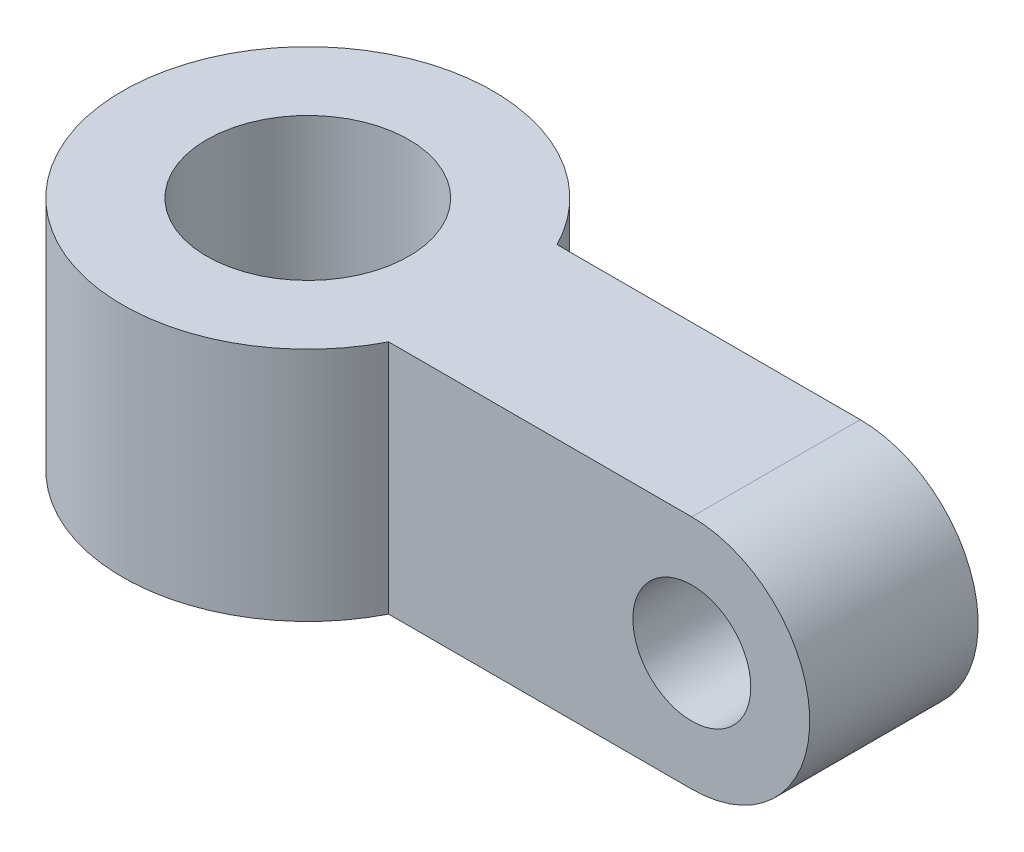
SolidWorks part; units mm, degrees
ref_plane "Plano frontal" through (0, 0, 0) normal (0, 0, 1) x (1, 0, 0)
ref_plane "Plano superior" through (0, 0, 0) normal (0, 1, 0) x (1, 0, 0)
ref_plane "Plano direito" through (0, 0, 0) normal (1, 0, 0) x (0, 0, -1)
sketch "Esboço1" plane through (0, 0, 0) normal (0, 0, 1) x (1, 0, 0)
  line L0 (-1.75, 0) -> (-6, 0) construction
  line L1 (0, 3.5) -> (-6, 3.5)
  line L2 (0, -3.5) -> (-6, -3.5)
  line L3 (-1.75, 3.5) -> (-6, 3.5) construction
  line L4 (-1.75, -3.5) -> (-6, -3.5) construction
  line L5 (-6, 3.5) -> (-6, -3.5)
  circle A0 centre (0, 0) radius 1.75
  arc A1 (0, -3.5) -> (0, 3.5) centre (0, 0) ccw
  dimension "D1" = 7
  dimension "D2" = 3.5
  dimension "D5" = 6
  dimension "D3" = 3.5
  dimension "D4" = 3.5
extrude "Ressalto-extrusão1" add sketch "Esboço1" along normal blind 5
sketch "Esboço2" plane through (0, 3.5, 0) normal (0, 1, 0) x (1, 0, 0)
  line L0 (-6, -2.5) -> (-13.899, -2.5) construction
  line L1 (-6, -5) -> (-6, 0) construction
  line L2 (-6, 0) -> (-9, 0)
  line L3 (-6, -5) -> (-9, -5)
  arc A0 (-9, 0) -> (-9, -5) centre (-13.899, -2.5) ccw
  circle A1 centre (-13.899, -2.5) radius 3
  dimension "D1" = 6
  dimension "D2" = 11
  dimension "D3" = 3
extrude "Ressalto-extrusão2" add sketch "Esboço2" against normal blind 7
